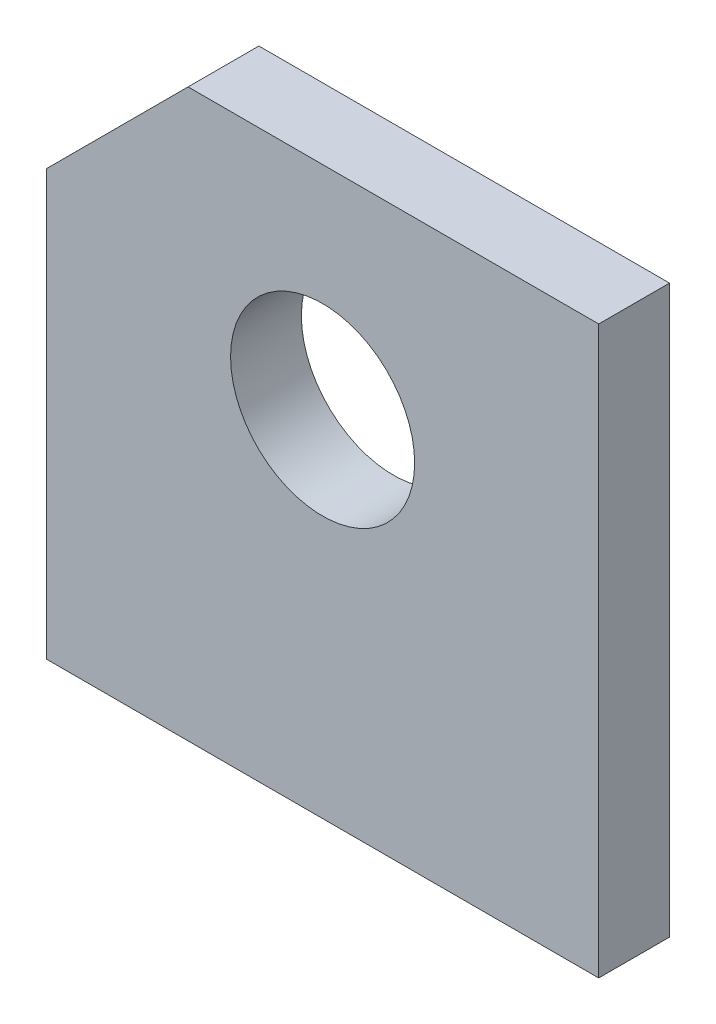
SolidWorks part; units mm, degrees
material "Oak"
ref_plane "Front" through (0, 0, 0) normal (0, 0, 1) x (1, 0, 0)
ref_plane "Top" through (0, 0, 0) normal (0, 1, 0) x (1, 0, 0)
ref_plane "Right" through (0, 0, 0) normal (1, 0, 0) x (0, 0, -1)
sketch "Sketch1" plane through (0, 0, 0) normal (0, 0, 1) x (1, 0, 0)
  line L0 (0, 15.24) -> (5.08, 20.32)
  line L1 (0, 0) -> (19.812, 0)
  line L2 (0, 0) -> (0, 15.24)
  line L3 (5.08, 20.32) -> (19.812, 20.32)
  line L4 (19.812, 0) -> (19.812, 20.32)
  circle A0 centre (9.906, 12.7) radius 3.302
  point P2 (0, 20.32)
  dimension "D4" = 6.604
  dimension "D1" = 19.812
  dimension "D2" = 20.32
  dimension "D3" = 12.7
extrude "Boss-Extrude1" add sketch "Sketch1" along normal blind 2.54
